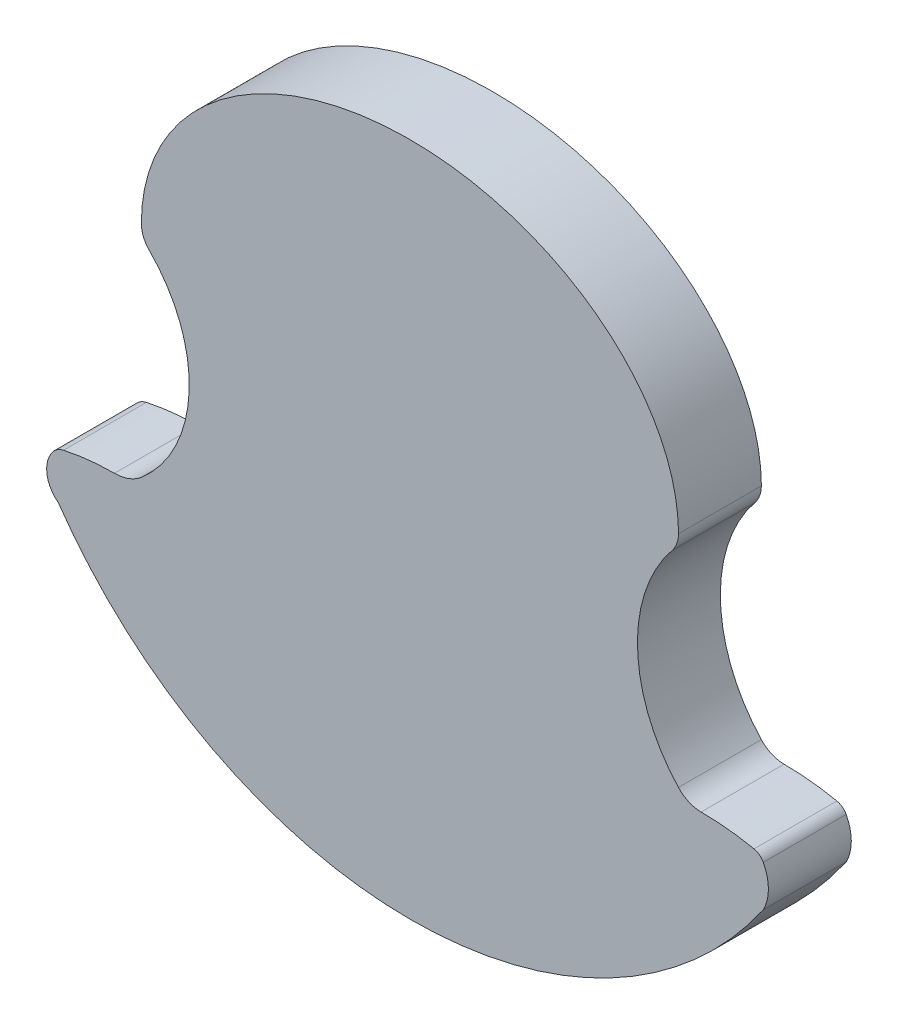
SolidWorks part; units mm, degrees
ref_plane "Plan de face" through (0, 0, 0) normal (0, 0, 1) x (1, 0, 0)
ref_plane "Plan de dessus" through (0, 0, 0) normal (0, 1, 0) x (1, 0, 0)
ref_plane "Plan de droite" through (0, 0, 0) normal (1, 0, 0) x (0, 0, -1)
sketch "Esquisse6" plane through (0, 0, 0) normal (0, 0, 1) x (1, 0, 0)
  line L0 (-57.2701, 162.2979) -> (-64.7925, 121.3971) construction
  line L1 (63.2961, 170.1986) -> (63.2961, 123.1192) construction
  line L10 (4.5, 164.3067) -> (4.5, 61.5672)
  line L11 (-7.6049, 164.3606) -> (-7.6049, 61.776)
  line L17 (-11.9055, 129.3227) -> (-11.9055, 154.3227)
  line L18 (8.9729, 154.354) -> (8.9729, 129.3227)
  arc A0 (64.7925, 174.3971) -> (59.4816, 167.8929) centre (58.1542, 174.3971) cw
  arc A1 (-64.7925, 174.3971) -> (-58.2883, 167.8929) centre (-58.2883, 174.3971) ccw
  arc A2 (-58.2883, 167.8929) -> (59.4816, 167.8929) centre (0.5967, 647.424) ccw
  arc A3 (-57.2701, 162.2979) -> (-11.9055, 154.3227) centre (49.8095, 638.378) ccw
  arc A4 (-62.8875, 169.7979) -> (-64.7925, 121.3971) centre (-86.2075, 146.4779) cw
  arc A5 (-66.0908, 120.4575) -> (-11.9055, 129.3227) centre (-10.6686, -48.2623) cw
  arc A6 (58.3516, 162.2979) -> (8.9729, 154.354) centre (-55.0751, 709.9055) cw
  arc A7 (8.9729, 129.3227) -> (66.0681, 120.2973) centre (2.1536, -98.9219) cw
  arc A8 (63.2961, 170.1986) -> (64.7925, 121.3971) centre (92.1251, 146.6589) ccw
  arc A9 (-64.7925, 121.3971) -> (-71.2859, 119.0021) centre (-71.2859, 129.0021) cw
  arc A10 (64.7925, 121.3971) -> (70.2674, 119.0021) centre (70.2674, 126.4572) ccw
  arc A11 (70.2674, 119.0021) -> (83.0175, 117.6775) centre (70.2674, 56.9734) cw
  arc A12 (83.0175, 117.6775) -> (85.2674, 115.9857) centre (82.335, 114.428) cw
  arc A13 (85.2674, 115.9857) -> (85.2674, 106.0843) centre (75.9474, 111.035) cw
  arc A14 (-71.2859, 119.0021) -> (-83.5684, 117.6775) centre (-71.2859, 61.3923) ccw
  arc A15 (-83.5684, 117.6775) -> (-86.2075, 115.9857) centre (-82.6076, 113.2746) ccw
  arc A16 (-86.2075, 115.9857) -> (-84.8131, 106.0843) centre (-80.5596, 111.7322) ccw
  arc A17 (-84.8131, 106.0843) -> (85.2674, 106.0843) centre (0.2272, 164.8461) ccw
  ellipse E0 centre (0, 174.3971) end of major axis (64.7925, 174.3971) minor radius 50 (0, 224.3971) -> (-64.7925, 174.3971) ccw
  ellipse E1 centre (0, 174.3971) end of major axis (64.7925, 174.3971) minor radius 50 (0, 224.3971) -> (64.7925, 174.3971) cw
  point P25 (0, 0)
  point P30 (0, 0)
  point P35 (0, 0)
  point P37 (0, 0)
  point P49 (0, 0)
  point P50 (0, 0)
extrude "Boss.-Extru.1" add sketch "Esquisse6" along normal blind 20 contours L11 A17 L10 A2 | L10 A17 A13 A12 A11 A10 A7 L18 A6 A8 A0 A2 | A10 A8 A6 L18 A7 | A16 A17 L11 A2 A1 A4 A3 L17 A5 A9 A14 A15 | A4 A9 A5 L17 A3 | E1 E0 A1 A2 A0
sketch3d "Esquisse3D1"
  point P0 (0.392, 61.4789, 8.7382)
sketch3d "Esquisse3D2" plane through (0, 0, 0) normal (0, 0, 1) x (1, 0, 0)
